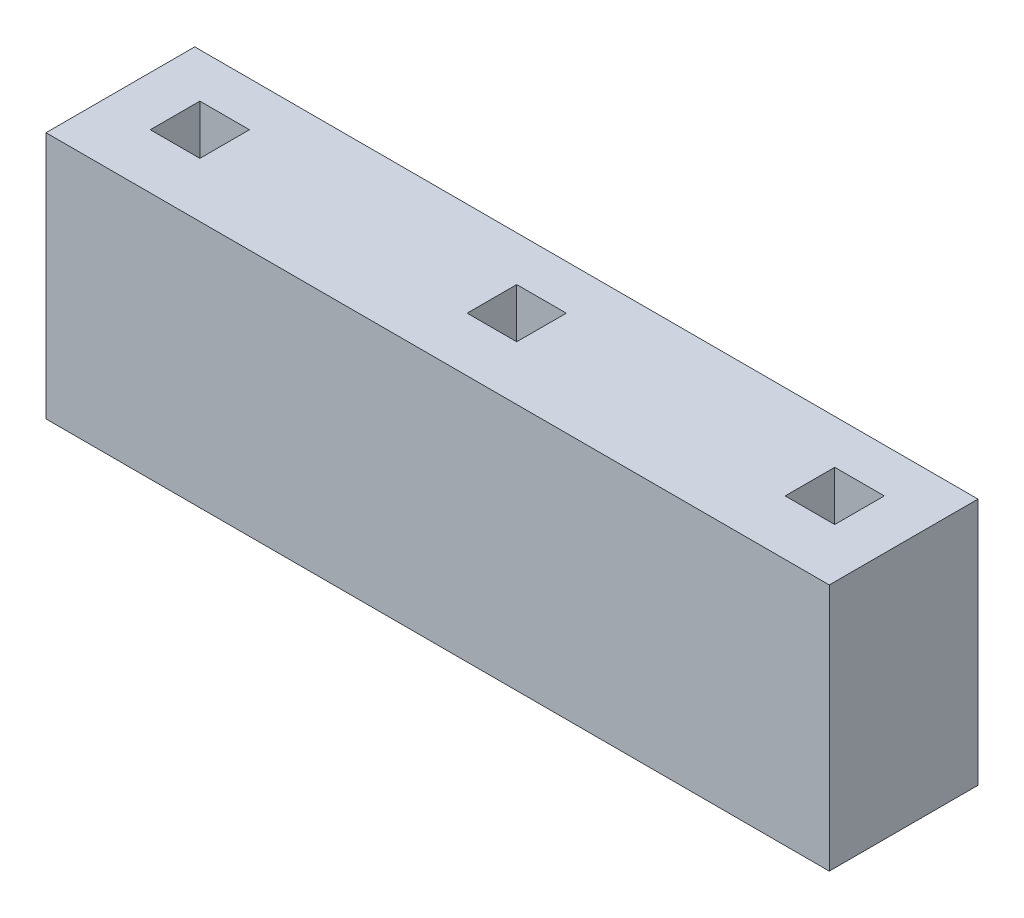
SolidWorks part; units mm, degrees
ref_plane "Front" through (0, 0, 0) normal (0, 0, 1) x (1, 0, 0)
ref_plane "Top" through (0, 0, 0) normal (0, 1, 0) x (1, 0, 0)
ref_plane "Right" through (0, 0, 0) normal (1, 0, 0) x (0, 0, -1)
sketch "Sketch1" plane through (0, 0, 0) normal (0, 1, 0) x (1, 0, 0)
  line L1 (-1.4449, 1.0143) -> (6.4551, 1.0143)
  line L2 (-1.4449, 1.0143) -> (-1.4449, -0.4857)
  line L3 (-1.4449, -0.4857) -> (6.4551, -0.4857)
  line L4 (6.4551, 1.0143) -> (6.4551, -0.4857)
  line L5 (-1.4449, 1.0143) -> (6.4551, -0.4857) construction
  line L6 (-1.4449, -0.4857) -> (6.4551, 1.0143) construction
  line L9 (-0.9449, 0.0662) -> (-0.4449, 0.0662)
  line L11 (-0.9449, 0.5662) -> (-0.9449, 0.0662)
  line L12 (-0.4449, 0.5662) -> (-0.4449, 0.0662)
  line L24 (5.4551, 0.0694) -> (5.9551, 0.0694)
  line L26 (5.4551, 0.5694) -> (5.4551, 0.0694)
  line L27 (5.9551, 0.5694) -> (5.9551, 0.0694)
  line L30 (-0.9449, 0.5662) -> (-0.4449, 0.5662)
  line L31 (5.4551, 0.5694) -> (5.9551, 0.5694)
  line L32 (2.2551, 0.5619) -> (2.7551, 0.5619)
  line L33 (2.2551, 0.5619) -> (2.2551, 0.0619)
  line L34 (2.2551, 0.0619) -> (2.7551, 0.0619)
  line L35 (2.7551, 0.5619) -> (2.7551, 0.0619)
  line L36 (5.9551, 0.5694) -> (6.4551, 0.5694)
  point P4 (2.5051, 0.2643)
  point P13 (0.7489, 0.4584)
  dimension "D2" = 1.5
  dimension "D3" = 0.5
  dimension "D4" = 2.7
  dimension "D5" = 2.7
  dimension "D6" = 0.5
  dimension "D7" = 0.5
  dimension "D8" = 0.5
  dimension "D9" = 0.5
  dimension "D12" = 0.5
extrude "Boss-Extrude1" add sketch "Sketch1" along normal blind 2.5 contours L4 L1 L2 L3 L11 L30 L12 L9 L26 L31 L27 L24 L32 L35 L34 L33
